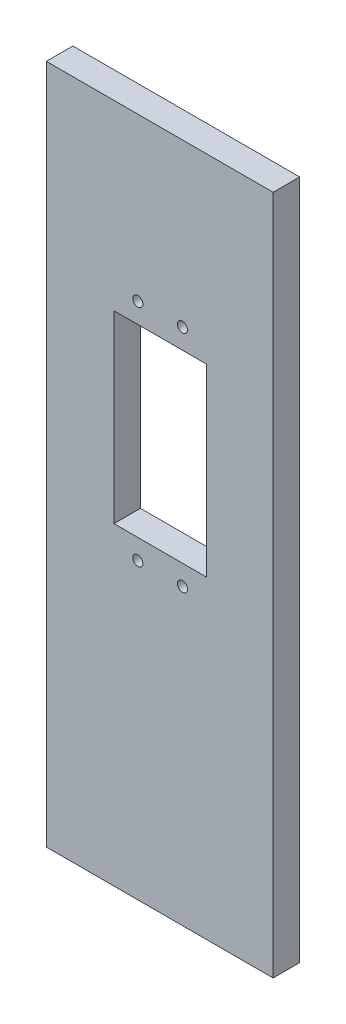
SolidWorks part; units mm, degrees
ref_plane "Front Plane" through (0, 0, 0) normal (0, 0, 1) x (1, 0, 0)
ref_plane "Top Plane" through (0, 0, 0) normal (0, 1, 0) x (1, 0, 0)
ref_plane "Right Plane" through (0, 0, 0) normal (1, 0, 0) x (0, 0, -1)
sketch "Sketch1" plane through (0, 0, 0) normal (0, 0, 1) x (1, 0, 0)
  line L1 (0, 0) -> (50.8, 0)
  line L2 (0, 0) -> (0, 152.4)
  line L3 (0, 152.4) -> (50.8, 152.4)
  line L4 (50.8, 0) -> (50.8, 152.4)
  dimension "D1" = 152.4
  dimension "D2" = 50.8
extrude "Boss-Extrude1" add sketch "Sketch1" along normal blind 5.9436
sketch "Sketch2" plane through (0, 0, 5.9436) normal (0, 0, 1) x (1, 0, 0)
  line L0 (25.4, 152.4) -> (25.4, 0) construction
  line L1 (50.8, 152.4) -> (0, 152.4) construction
  line L2 (0, 0) -> (50.8, 0) construction
  line L4 (15.1421, 111.6) -> (35.8421, 111.6)
  line L5 (15.1421, 111.6) -> (15.1421, 70.3)
  line L6 (15.1421, 70.3) -> (35.8421, 70.3)
  line L7 (35.8421, 111.6) -> (35.8421, 70.3)
  circle A1 centre (20.4921, 116.1) radius 1.1303
  circle A2 centre (30.4921, 116.1) radius 1.1303
  circle A3 centre (20.4921, 65.8) radius 1.1303
  circle A4 centre (30.4921, 65.8) radius 1.1303
  dimension "D1" = 2.2606
extrude "Cut-Extrude1" cut sketch "Sketch2" against normal through all
